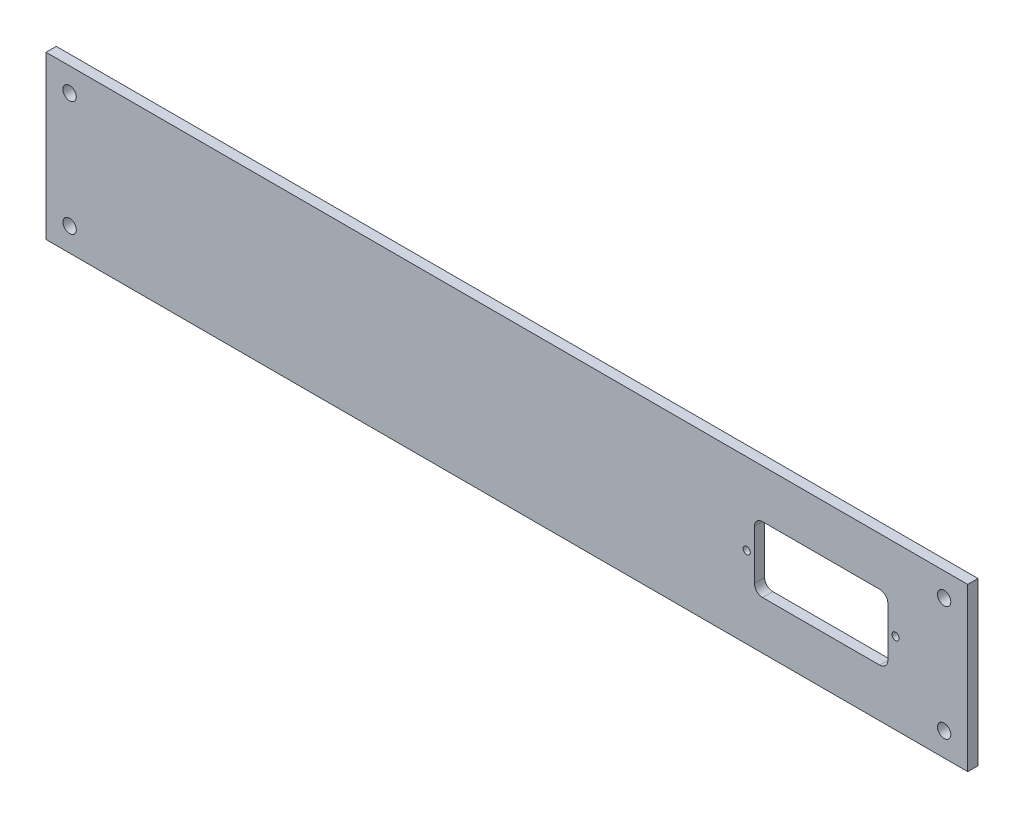
SolidWorks part; units mm, degrees
ref_plane "Piano frontale" through (0, 0, 0) normal (0, 0, 1) x (1, 0, 0)
ref_plane "Piano superiore" through (0, 0, 0) normal (0, 1, 0) x (1, 0, 0)
ref_plane "Piano destro" through (0, 0, 0) normal (1, 0, 0) x (0, 0, -1)
sketch "f" plane through (0, 0, 0) normal (0, 0, 1) x (1, 0, 0)
  line L0 (0, 0) -> (0, 79)
  line L1 (0, 79) -> (449, 79)
  line L2 (449, 79) -> (449, 0)
  line L3 (449, 0) -> (0, 0)
  line L4 (0, 39.5) -> (449, 39.5) construction
  line L5 (224.5, 42) -> (224.5, 123.488) construction
  line L10 (449, 79) -> (224.5, 0) construction
  line L11 (334, 39.5) -> (334, 81.5) construction
  line L12 (224.5, 0) -> (0, 79) construction
  line L13 (112.25, 42) -> (112.25, 84) construction
  circle A0 centre (11.5, 67.5) radius 3.25
  circle A1 centre (437.5, 67.5) radius 3.25
  circle A2 centre (11.5, 11.5) radius 3.25
  circle A3 centre (437.5, 11.5) radius 3.25
  dimension "D3" = 11.5
  dimension "D4" = 11.5
  dimension "D5" = 6.5
  dimension "D1" = 79
  dimension "D2" = 449
extrude "Estrusione-Estrusione1" add sketch "f" along normal blind 5
sketch "Sketch1" plane through (0, 0, 0) normal (0, 0, -1) x (-1, 0, 0)
  line L0 (0, 39.5) -> (-449, 39.5) construction
  line L1 (0, 79) -> (0, 0) construction
  line L2 (-449, 0) -> (-449, 79) construction
  line L3 (-377.5746, 55.5) -> (-377.5746, 23.5) construction
  line L7 (-349.0746, 55.5) -> (-406.0746, 55.5)
  line L8 (-345.0746, 51.5) -> (-345.0746, 27.5)
  line L9 (-349.0746, 23.5) -> (-406.0746, 23.5)
  line L10 (-410.0746, 51.5) -> (-410.0746, 27.5)
  circle A0 centre (-341.3246, 39.5055) radius 1.75
  arc A4 (-345.0746, 51.5) -> (-349.0746, 55.5) centre (-349.0746, 51.5) ccw
  arc A5 (-345.0746, 27.5) -> (-349.0746, 23.5) centre (-349.0746, 27.5) cw
  arc A6 (-406.0746, 23.5) -> (-410.0746, 27.5) centre (-406.0746, 27.5) cw
  arc A7 (-410.0746, 51.5) -> (-406.0746, 55.5) centre (-406.0746, 51.5) cw
  circle A8 centre (-413.8246, 39.5055) radius 1.75
  dimension "D1" = 16
  dimension "D4" = 3.5
  dimension "D2" = 65
  dimension "D3" = 36.25
extrude "Extrude1" cut sketch "Sketch1" against normal through all
